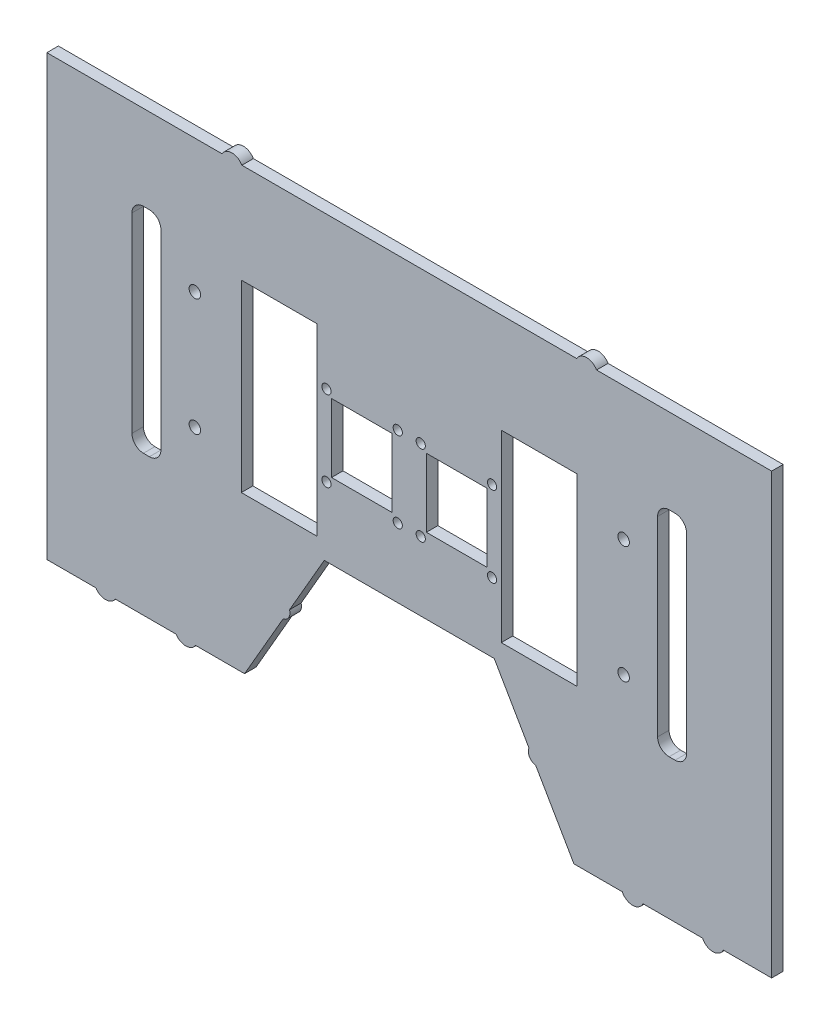
SolidWorks part; units mm, degrees
ref_plane "Front Plane" through (0, 0, 0) normal (0, 0, 1) x (1, 0, 0)
ref_plane "Top Plane" through (0, 0, 0) normal (0, 1, 0) x (1, 0, 0)
ref_plane "Right Plane" through (0, 0, 0) normal (1, 0, 0) x (0, 0, -1)
sketch "Sketch1" plane through (0, 0, 0) normal (0, 0, 1) x (1, 0, 0)
  line L188 (144.5813, -34.6657) -> (147.1813, -34.6657) construction
  line L201 (-8.3887, 51.8271) -> (-41.3887, 51.8271)
  line L202 (-8.3887, 51.8271) -> (-8.3887, -28.1729)
  line L203 (-8.3887, -28.1729) -> (-41.3887, -28.1729)
  line L204 (-41.3887, 51.8271) -> (-41.3887, -28.1729)
  line L205 (-8.3887, 51.8271) -> (-41.3887, -28.1729) construction
  line L206 (-8.3887, -28.1729) -> (-41.3887, 51.8271) construction
  line L207 (104.6113, 51.8271) -> (71.6113, 51.8271)
  line L208 (104.6113, 51.8271) -> (104.6113, -28.1729)
  line L209 (104.6113, -28.1729) -> (71.6113, -28.1729)
  line L210 (71.6113, 51.8271) -> (71.6113, -28.1729)
  line L211 (104.6113, 51.8271) -> (71.6113, -28.1729) construction
  line L212 (104.6113, -28.1729) -> (71.6113, 51.8271) construction
  line L213 (147.1813, 58.3199) -> (144.5813, 58.3199) construction
  line L214 (139.5813, 53.3199) -> (139.5813, -29.6657) construction
  line L215 (152.1813, -29.6657) -> (152.1813, 53.3199) construction
  line L216 (144.5813, -34.6657) -> (147.1813, -34.6657)
  line L217 (147.1813, 58.3199) -> (144.5813, 58.3199)
  line L218 (139.5813, 53.3199) -> (139.5813, -29.6657)
  line L219 (152.1813, -29.6657) -> (152.1813, 53.3199)
  line L220 (-83.9587, -34.6657) -> (-81.3587, -34.6657) construction
  line L221 (-88.9587, 53.3199) -> (-88.9587, -29.6657) construction
  line L222 (-76.3587, -29.6657) -> (-76.3587, 53.3199) construction
  line L223 (-81.3587, 58.3199) -> (-83.9587, 58.3199) construction
  line L224 (-83.9587, -34.6657) -> (-81.3587, -34.6657)
  line L225 (-88.9587, 53.3199) -> (-88.9587, -29.6657)
  line L226 (-76.3587, -29.6657) -> (-76.3587, 53.3199)
  line L227 (-81.3587, 58.3199) -> (-83.9587, 58.3199)
  line L244 (-125.94, -95.6729) -> (-104.6358, -95.6729)
  line L245 (-125.94, 95.1805) -> (-125.94, -95.6729)
  line L246 (-49.8198, 95.1805) -> (-125.94, 95.1805)
  line L247 (104.3821, 95.1805) -> (-41.1595, 95.1805)
  line L248 (189.1626, 95.1805) -> (113.0424, 95.1805)
  line L249 (189.1626, -95.6729) -> (189.1626, 95.1805)
  line L250 (168.1491, -95.6729) -> (189.1626, -95.6729)
  line L251 (133.2564, -95.6729) -> (159.1089, -95.6729)
  line L252 (103.2027, -95.6729) -> (124.2161, -95.6729)
  line L253 (86.5983, -66.9132) -> (103.2027, -95.6729)
  line L254 (68.5617, -35.6729) -> (83.6511, -61.8085)
  line L255 (-5.3392, -35.6729) -> (68.5617, -35.6729)
  line L256 (-20.4397, -61.8279) -> (-5.3392, -35.6729)
  line L257 (-39.9802, -95.6729) -> (-23.2348, -66.6691)
  line L258 (-61.2844, -95.6729) -> (-39.9802, -95.6729)
  line L259 (-96.1754, -95.6729) -> (-69.7448, -95.6729)
  line L260 (-125.94, -95.6729) -> (-104.6358, -95.6729)
  line L261 (-125.94, 95.1805) -> (-125.94, -95.6729)
  line L262 (-49.8198, 95.1805) -> (-125.94, 95.1805)
  line L263 (104.3821, 95.1805) -> (-41.1595, 95.1805)
  line L264 (189.1626, 95.1805) -> (113.0424, 95.1805)
  line L265 (189.1626, -95.6729) -> (189.1626, 95.1805)
  line L266 (168.1491, -95.6729) -> (189.1626, -95.6729)
  line L267 (133.2564, -95.6729) -> (159.1089, -95.6729)
  line L268 (103.2027, -95.6729) -> (124.2161, -95.6729)
  line L269 (86.5983, -66.9132) -> (103.2027, -95.6729)
  line L270 (68.5617, -35.6729) -> (83.6511, -61.8085)
  line L271 (-5.3392, -35.6729) -> (68.5617, -35.6729)
  line L272 (-20.4397, -61.8279) -> (-5.3392, -35.6729)
  line L273 (-39.9802, -95.6729) -> (-23.2348, -66.6691)
  line L274 (-61.2844, -95.6729) -> (-39.9802, -95.6729)
  line L275 (-96.1754, -95.6729) -> (-69.7448, -95.6729)
  line L308 (31.6113, 95.1805) -> (31.6113, 107.1248) construction
  line L309 (39.059, 26.8505) -> (39.059, -2.9094)
  line L310 (24.1636, 26.8505) -> (-2.1951, 26.8505)
  line L311 (24.1636, 26.8505) -> (24.1636, -2.9094)
  line L312 (24.1636, -2.9094) -> (-2.1951, -2.9094)
  line L313 (-2.1951, 26.8505) -> (-2.1951, -2.9094)
  line L314 (24.1636, 26.8505) -> (-2.1951, -2.9094) construction
  line L315 (24.1636, -2.9094) -> (-2.1951, 26.8505) construction
  line L316 (-4.3887, 29.3271) -> (26.6113, -5.6729) construction
  line L317 (39.059, -2.9094) -> (65.4178, -2.9094)
  line L318 (65.4178, 26.8505) -> (65.4178, -2.9094)
  line L319 (39.059, 26.8505) -> (65.4178, 26.8505)
  arc A39 (147.1813, -34.6657) -> (152.1813, -29.6657) centre (147.1813, -29.6657) ccw construction
  arc A40 (139.5813, -29.6657) -> (144.5813, -34.6657) centre (144.5813, -29.6657) ccw construction
  arc A41 (152.1813, 53.3199) -> (147.1813, 58.3199) centre (147.1813, 53.3199) ccw construction
  arc A42 (144.5813, 58.3199) -> (139.5813, 53.3199) centre (144.5813, 53.3199) ccw construction
  arc A43 (147.1813, -34.6657) -> (152.1813, -29.6657) centre (147.1813, -29.6657) ccw
  arc A44 (139.5813, -29.6657) -> (144.5813, -34.6657) centre (144.5813, -29.6657) ccw
  arc A45 (152.1813, 53.3199) -> (147.1813, 58.3199) centre (147.1813, 53.3199) ccw
  arc A46 (144.5813, 58.3199) -> (139.5813, 53.3199) centre (144.5813, 53.3199) ccw
  arc A47 (-81.3587, -34.6657) -> (-76.3587, -29.6657) centre (-81.3587, -29.6657) ccw construction
  arc A48 (-88.9587, -29.6657) -> (-83.9587, -34.6657) centre (-83.9587, -29.6657) ccw construction
  arc A49 (-76.3587, 53.3199) -> (-81.3587, 58.3199) centre (-81.3587, 53.3199) ccw construction
  arc A50 (-83.9587, 58.3199) -> (-88.9587, 53.3199) centre (-83.9587, 53.3199) ccw construction
  arc A51 (-81.3587, -34.6657) -> (-76.3587, -29.6657) centre (-81.3587, -29.6657) ccw
  arc A52 (-88.9587, -29.6657) -> (-83.9587, -34.6657) centre (-83.9587, -29.6657) ccw
  arc A53 (-76.3587, 53.3199) -> (-81.3587, 58.3199) centre (-81.3587, 53.3199) ccw
  arc A54 (-83.9587, 58.3199) -> (-88.9587, 53.3199) centre (-83.9587, 53.3199) ccw
  circle A55 centre (67.6113, 29.3271) radius 2
  circle A56 centre (36.6113, 29.3271) radius 2
  circle A57 centre (26.6113, 29.3271) radius 2
  circle A58 centre (-4.3887, 29.3271) radius 2
  circle A59 centre (67.6113, -5.6729) radius 2
  circle A60 centre (36.6113, -5.6729) radius 2
  circle A61 centre (26.6113, -5.6729) radius 2
  circle A62 centre (-4.3887, -5.6729) radius 2
  circle A63 centre (-61.5887, -13.6729) radius 2.5
  circle A64 centre (-61.5887, 37.3271) radius 2.5
  circle A65 centre (124.8113, 37.3271) radius 2.5
  circle A66 centre (124.8113, -13.6729) radius 2.5
  arc A75 (-104.6358, -95.6729) -> (-96.1754, -95.6729) centre (-100.4056, -93.0073) ccw
  arc A76 (-41.1595, 95.1805) -> (-49.8198, 95.1805) centre (-45.4897, 92.6805) ccw
  arc A77 (113.0424, 95.1805) -> (104.3821, 95.1805) centre (108.7123, 92.6805) ccw
  arc A78 (159.1089, -95.6729) -> (168.1491, -95.6729) centre (163.629, -93.5355) ccw
  arc A79 (124.2161, -95.6729) -> (133.2564, -95.6729) centre (128.7363, -93.5355) ccw
  arc A80 (83.6511, -61.8085) -> (86.5983, -66.9132) centre (87.1327, -63.2015) ccw
  arc A81 (-23.2348, -66.6691) -> (-20.4397, -61.8279) centre (-24.0023, -62.9985) ccw
  arc A82 (-69.7448, -95.6729) -> (-61.2844, -95.6729) centre (-65.5146, -93.0073) ccw
  arc A83 (-104.6358, -95.6729) -> (-96.1754, -95.6729) centre (-100.4056, -93.0073) ccw
  arc A84 (-41.1595, 95.1805) -> (-49.8198, 95.1805) centre (-45.4897, 92.6805) ccw
  arc A85 (113.0424, 95.1805) -> (104.3821, 95.1805) centre (108.7123, 92.6805) ccw
  arc A86 (159.1089, -95.6729) -> (168.1491, -95.6729) centre (163.629, -93.5355) ccw
  arc A87 (124.2161, -95.6729) -> (133.2564, -95.6729) centre (128.7363, -93.5355) ccw
  arc A88 (83.6511, -61.8085) -> (86.5983, -66.9132) centre (87.1327, -63.2015) ccw
  arc A89 (-23.2348, -66.6691) -> (-20.4397, -61.8279) centre (-24.0023, -62.9985) ccw
  arc A90 (-69.7448, -95.6729) -> (-61.2844, -95.6729) centre (-65.5146, -93.0073) ccw
  point P4 (50.9304, 11.1392)
  point P9 (10.9842, 11.9705)
  point P14 (-24.8887, 11.8271)
  point P19 (88.1113, 11.8271)
  dimension "D1" = 0
extrude "Boss-Extrude1" add sketch "Sketch1" along normal blind 5
